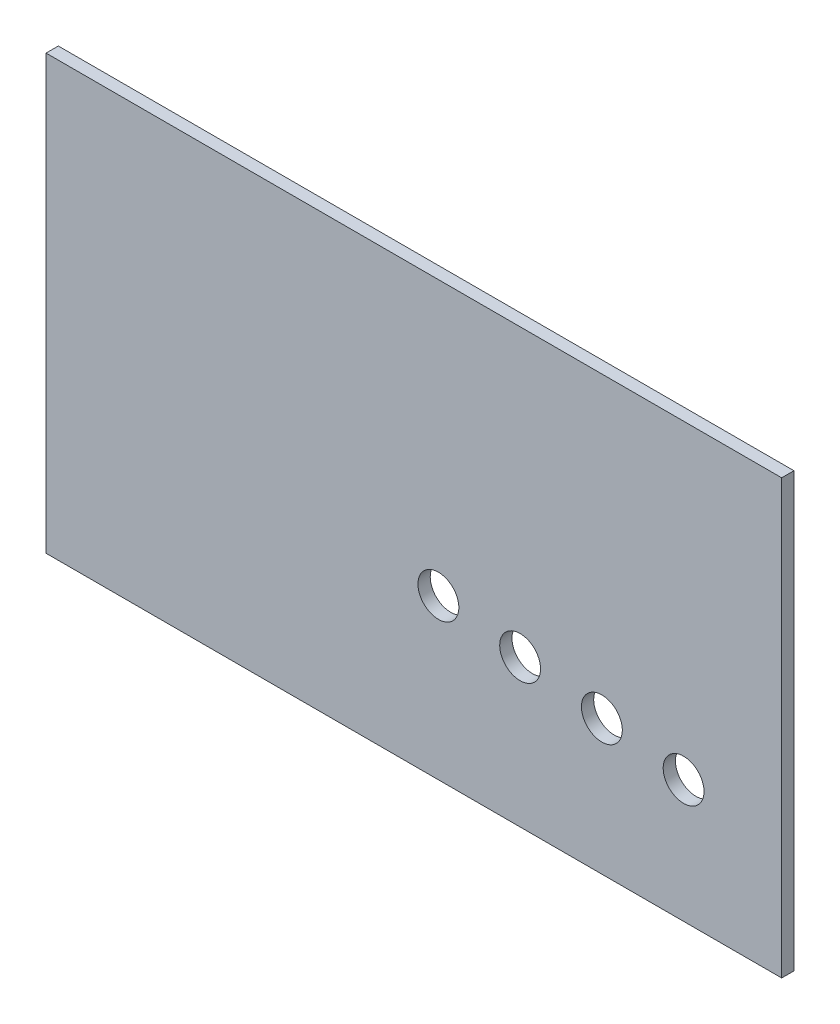
SolidWorks part; units mm, degrees
material "Balsa"
ref_plane "Front Plane" through (0, 0, 0) normal (0, 0, 1) x (1, 0, 0)
ref_plane "Top Plane" through (0, 0, 0) normal (0, 1, 0) x (1, 0, 0)
ref_plane "Right Plane" through (0, 0, 0) normal (1, 0, 0) x (0, 0, -1)
sketch "Sketch1" plane through (0, 0, 0) normal (0, 0, 1) x (1, 0, 0)
  line L1 (0, 0) -> (900, 0)
  line L2 (0, 0) -> (0, 530)
  line L3 (0, 530) -> (900, 530)
  line L4 (900, 0) -> (900, 530)
  dimension "D1" = 900
  dimension "D2" = 530
extrude "Boss-Extrude1" add sketch "Sketch1" along normal blind 15
sketch "Sketch3" plane through (0, 0, 0) normal (0, 0, -1) x (-1, 0, 0)
  line L0 (-900, 0) -> (-900, 530) construction
  line L1 (0, 0) -> (-900, 0) construction
  circle A0 centre (-780, 150) radius 25
  circle A4 centre (-680, 165) radius 25
  circle A5 centre (-580, 180) radius 25
  circle A6 centre (-480, 195) radius 25
  dimension "D1" = 50
  dimension "D2" = 50
  dimension "D5" = 50
  dimension "D6" = 50
  dimension "D3" = 120
  dimension "D4" = 150
  dimension "D7" = 100
  dimension "D8" = 100
  dimension "D9" = 100
  dimension "D10" = 165
  dimension "D11" = 180
  dimension "D12" = 195
extrude "Cut-Extrude1" cut sketch "Sketch3" against normal through all
